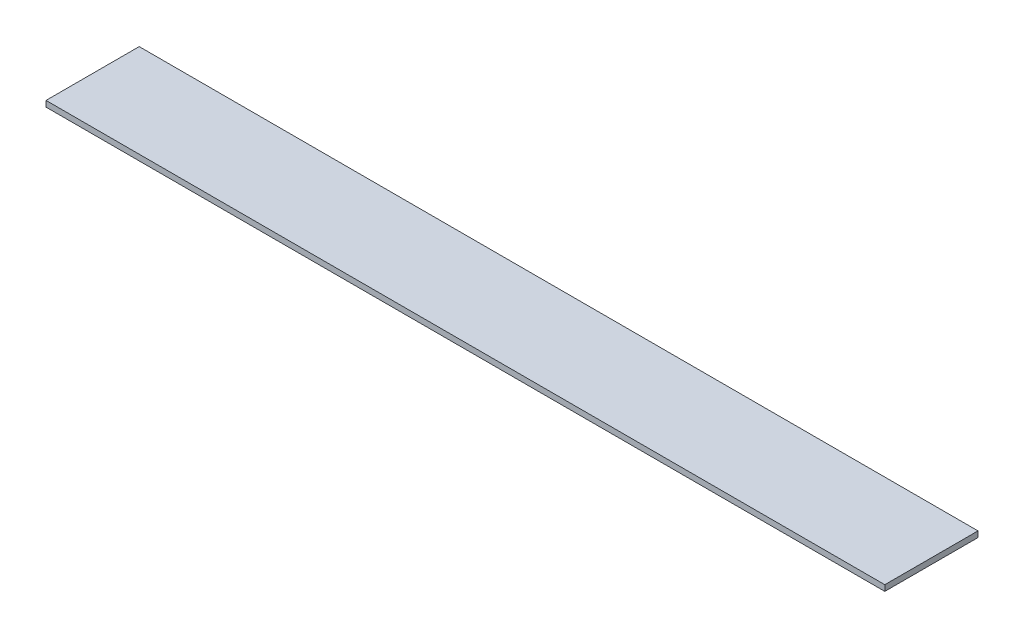
SolidWorks part; units mm, degrees
ref_plane "Front Plane" through (0, 0, 0) normal (0, 0, 1) x (1, 0, 0)
ref_plane "Top Plane" through (0, 0, 0) normal (0, 1, 0) x (1, 0, 0)
ref_plane "Right Plane" through (0, 0, 0) normal (1, 0, 0) x (0, 0, -1)
sketch "Sketch1" plane through (0, 0, 0) normal (0, 1, 0) x (1, 0, 0)
  line L1 (0, 0) -> (228.6, 0)
  line L2 (0, 0) -> (0, 25.4)
  line L3 (0, 25.4) -> (228.6, 25.4)
  line L4 (228.6, 0) -> (228.6, 25.4)
  dimension "D1" = 25.4
  dimension "D2" = 228.6
extrude "Boss-Extrude1" add sketch "Sketch1" along normal blind 1.5875
